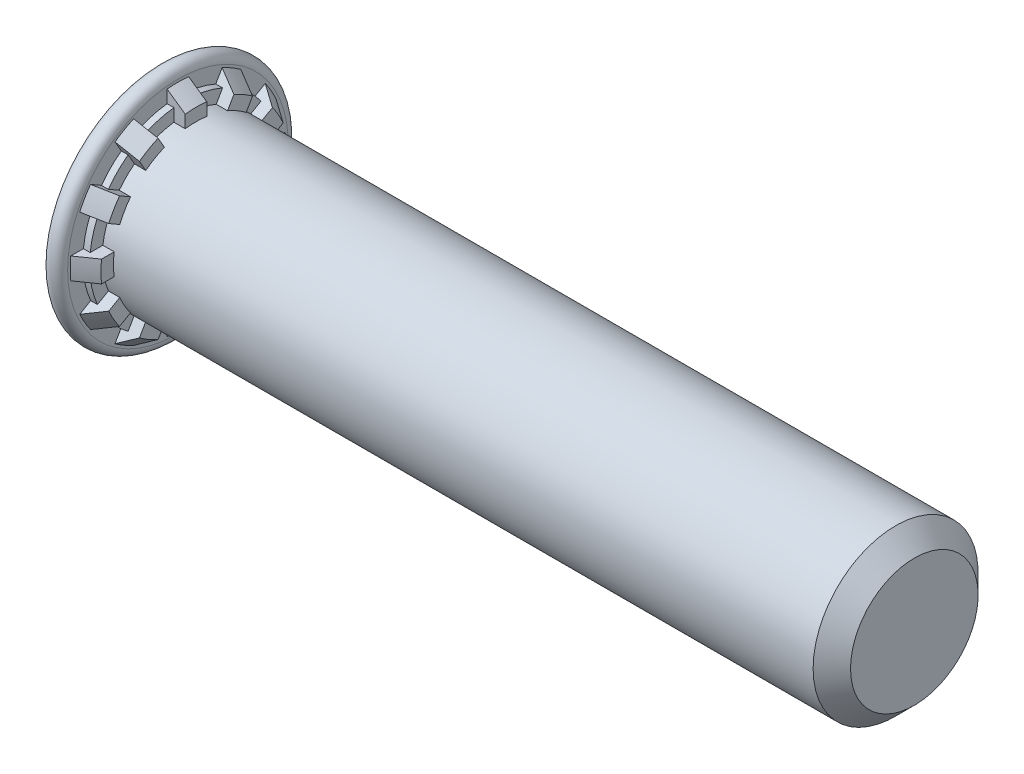
SolidWorks part; units mm, degrees
ref_plane "Plane1" through (0, 0, 0) normal (0, 0, 1) x (1, 0, 0)
ref_plane "Plane2" through (0, 0, 0) normal (0, 1, 0) x (1, 0, 0)
ref_plane "Plane3" through (0, 0, 0) normal (1, 0, 0) x (0, 0, -1)
sketch "BodySke" plane through (0, 0, 0) normal (0, 0, 1) x (1, 0, 0)
  line L0 (0, 0) -> (0, 2.7788)
  line L1 (0.4572, 2.7838) -> (0.4572, 2.7178)
  line L2 (0.4572, 2.7178) -> (0.9144, 2.4003)
  line L3 (0.9144, 2.0828) -> (18.5776, 2.0828)
  line L4 (19.05, 1.6104) -> (19.05, 0)
  line L5 (19.05, 0) -> (0, 0)
  line L6 (0, 0) -> (50.554, 0) construction
  line L7 (0.9144, 2.4003) -> (0.9144, 2.0828)
  line L8 (19.05, 1.6104) -> (18.5776, 2.0828)
  line L9 (-9.525, 3.0099) -> (9.525, 3.0099) construction
  line L11 (1.7069, 19.05) -> (1.7069, -3.175) construction
  line L13 (9.525, -3.0099) -> (-9.525, -3.0099) construction
  line L14 (0.0051, 2.7838) -> (0.0051, 2.7788)
  line L15 (0, 2.7788) -> (0.0051, 2.7788)
  arc A0 (0.0051, 2.7838) -> (0.4572, 2.7838) centre (0.2311, 2.7838) cw
  dimension "D2" = 0.0051
  dimension "D1" = 0.0051
  dimension "Diameter" = 4.1656
  dimension "Length" = 19.05
  dimension "Body_ch_ang" = 45
  dimension "Minor_dia" = 3.2207
  dimension "Advance" = 0.7925
  dimension "H_dia" = 6.0198
  dimension "Shoulder_lower_dia" = 5.4356
  dimension "Shoulder_upper_dia" = 4.8006
  dimension "Shoulder_ht" = 0.9144
  dimension "T_dim" = 0.4572
revolve "BaseBody" add sketch "BodySke" angle 360 about L6
cosmetic thread "ThreadCosmetic" [suppressed] parameters "Thread_length"=16.764, "Thread_minor"=3.2207
sketch "ThdSchSke" plane through (0, 0, 0) normal (0, 0, 1) x (1, 0, 0)
  line L0 (2.286, -1.6104) -> (1.9552, -2.0828)
  line L1 (2.286, -1.6104) -> (2.6168, -2.0828)
  line L2 (2.6168, -2.0828) -> (2.6168, -2.6035)
  line L3 (-3.175, 0) -> (5.1513, 0) construction
  line L5 (2.6168, -2.6035) -> (1.9552, -2.6035)
  line L6 (1.9552, -2.6035) -> (1.9552, -2.0828)
  line L7 (0, 2.7788) -> (0, -2.7788) construction
  dimension "Thread_minor" = 3.2207
  dimension "Diameter" = 4.1656
  dimension "Start" = 2.286
  dimension "SideAngle" = 55
  dimension "VeeAngle" = 70
  dimension "Overcut" = 5.207
revolve "ThreadSchematic" [suppressed] cut sketch "ThdSchSke" angle 360 about L3
pattern_linear "ThdSchPat" [suppressed]
sketch "RibCut1Ske" plane through (0.9144, 0, 0) normal (1, 0, 0) x (0, 0, -1)
  line L0 (0.2719, 2.065) -> (0.2719, 2.9976)
  line L1 (0.7971, 1.9243) -> (1.2634, 2.7319)
  line L2 (0, 0) -> (0, 4.9784) construction
  line L3 (0, 0) -> (0.2719, 2.065) construction
  line L4 (0, 0) -> (0.7971, 1.9243) construction
  arc A1 (0.7971, 1.9243) -> (0.2719, 2.065) centre (0, 0) ccw
  arc A2 (1.2634, 2.7319) -> (0.2719, 2.9976) centre (0, 0) ccw
  dimension "Inner_dia" = 4.1656
  dimension "Outer_dia" = 6.0198
  dimension "Rib_root_half_angle" = 7.5
  dimension "Rib_root_gap_angle" = 15
  dimension "Angle" = 30
extrude "RibCut1" cut sketch "RibCut1Ske" against normal blind 0.2858
sketch "RibCut2Ske" plane through (0.9144, 0, 0) normal (1, 0, 0) x (0, 0, -1)
  line L0 (0.2719, 2.3849) -> (0.2719, 2.9976)
  line L1 (0.957, 2.2013) -> (1.2634, 2.7319)
  line L2 (0.2719, 2.065) -> (0.2719, 3.8767) construction
  line L3 (0, 0) -> (0, 5.0239) construction
  line L4 (0, 0) -> (0.2719, 2.065) construction
  line L5 (0, 0) -> (0.7971, 1.9243) construction
  line L6 (0.7971, 1.9243) -> (1.7065, 3.4994) construction
  arc A1 (0.957, 2.2013) -> (0.2719, 2.3849) centre (0, 0) ccw
  arc A2 (1.2634, 2.7319) -> (0.2719, 2.9976) centre (0, 0) ccw
  circle A4 centre (0, 0) radius 2.0828 construction
  dimension "Inner_dia" = 4.8006
  dimension "Outer_dia" = 6.0198
  dimension "Rib_root_dia" = 4.1656
  dimension "Rib_root_half_angle" = 7.5
  dimension "Rib_root_gap_angle" = 15
  dimension "Angle" = 30
extrude "RibCut2" cut sketch "RibCut2Ske" against normal blind 0.4572
pattern_circular "RibCutsPat" count 12 every 30 about axis through (0, 0, 0) along (1, 0, 0) of "RibCut2", "RibCut1"
equation "' \"Length@BodySke\" = 0.75"
equation "' \"H_dia@BodySke\" = 0.337"
equation "' \"Start@ThdSchSke\" = 0.135"
equation "' \"Diameter@BodySke\" = 0.25"
equation "' \"Minor_dia@BodySke\" =0.1905"
equation "' \"Advance@BodySke\" = 0.05"
equation "\"T_dim@BodySke\" = \"Start@ThdSchSke\" * 0.2"
equation "\"Shoulder_ht@BodySke\" = \"Start@ThdSchSke\" * 0.4"
equation "\"Shoulder_lower_dia@BodySke\" = \"H_dia@BodySke\" - \"Start@ThdSchSke\" * 0.2 - .005"
equation "\"Shoulder_upper_dia@BodySke\" = ( \"Shoulder_lower_dia@BodySke\" + \"Diameter@BodySke\" ) /2"
equation "\"Num_ribs@RibCutsPat\" = 12"
equation "\"Angle@RibCutsPat\" = 360 / \"Num_ribs@RibCutsPat\""
equation "\"Angle@RibCut1Ske\" =\"Angle@RibCutsPat\""
equation "\"Rib_root_half_angle@RibCut1Ske\" = \"Angle@RibCut1Ske\" / 4"
equation "\"Rib_root_gap_angle@RibCut1Ske\" = \"Angle@RibCut1Ske\" - (2 * \"Rib_root_half_angle@RibCut1Ske\" )"
equation "\"Inner_dia@RibCut1Ske\" = \"Diameter@BodySke\""
equation "\"Outer_dia@RibCut1Ske\" = \"H_dia@BodySke\""
equation "\"Depth@RibCut1\" =  \"Start@ThdSchSke\" * 0.125"
equation "\"Angle@RibCut2Ske\" =\"Angle@RibCutsPat\""
equation "\"Rib_root_half_angle@RibCut2Ske\" = \"Angle@RibCut1Ske\" / 4"
equation "\"Rib_root_gap_angle@RibCut2Ske\" = \"Angle@RibCut1Ske\" - (2 * \"Rib_root_half_angle@RibCut1Ske\" )"
equation "\"Rib_root_dia@RibCut2Ske\" = \"Diameter@BodySke\""
equation "\"Inner_dia@RibCut2Ske\" = \"Shoulder_upper_dia@BodySke\""
equation "\"Outer_dia@RibCut2Ske\" = \"H_dia@BodySke\""
equation "\"Depth@RibCut2\" =  \"Start@ThdSchSke\" * 0.2"
equation "\"Thread_length@ThreadCosmetic\" = \"Length@BodySke\" - \"Start@ThdSchSke\""
equation "\"Thread_minor@ThreadCosmetic\" = \"Minor_dia@BodySke\""
equation "\"Thread_minor@ThdSchSke\" = \"Minor_dia@BodySke\""
equation "\"Diameter@ThdSchSke\" = \"Diameter@BodySke\""
equation "\"Overcut@ThdSchSke\" = \"Diameter@BodySke\" * 1.25"
equation "\"Num_threads@ThdSchPat\" = int( \"Thread_length@ThreadCosmetic\" / \"Advance@BodySke\" + 0.999 )  + 1"
equation "\"Advance@ThdSchPat\" = \"Thread_length@ThreadCosmetic\" /  (\"Num_threads@ThdSchPat\" - 1) 'relax it"
equation "\"Num_threads@ThdSchPat\" = \"Num_threads@ThdSchPat\" - sgn( \"Num_threads@ThdSchPat\" - 1) '---chamfered tips only---"
